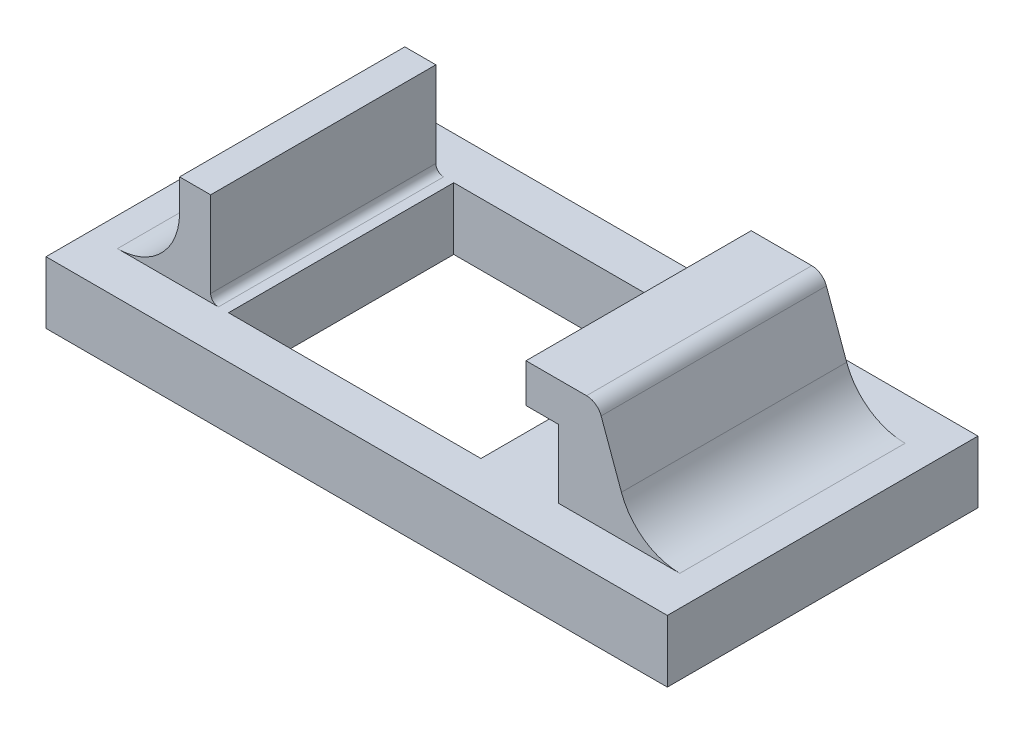
SolidWorks part; units mm, degrees
ref_plane "Front Plane" through (0, 0, 0) normal (0, 0, 1) x (1, 0, 0)
ref_plane "Top Plane" through (0, 0, 0) normal (0, 1, 0) x (1, 0, 0)
ref_plane "Right Plane" through (0, 0, 0) normal (1, 0, 0) x (0, 0, -1)
sketch "Sketch1" plane through (0, 0, 0) normal (0, 1, 0) x (1, 0, 0)
  line L1 (-20, 10) -> (20, 10)
  line L2 (-20, 10) -> (-20, -10)
  line L3 (-20, -10) -> (20, -10)
  line L4 (20, 10) -> (20, -10)
  line L5 (-20, 10) -> (20, -10) construction
  line L6 (-20, -10) -> (20, 10) construction
  point P0 (0, 0)
  dimension "D1" = 40
  dimension "D2" = 20
extrude "Boss-Extrude1" add sketch "Sketch1" along normal blind 4
sketch "Sketch2" plane through (0, 4, 0) normal (0, 1, 0) x (1, 0, 0)
  line L0 (-20, 10) -> (-20, -10) construction
  line L1 (-11, 7.25) -> (5.25, 7.25)
  line L2 (-11, 7.25) -> (-11, -7.25)
  line L3 (-11, -7.25) -> (5.25, -7.25)
  line L4 (5.25, 7.25) -> (5.25, -7.25)
  line L5 (-11, 7.25) -> (5.25, -7.25) construction
  line L6 (-11, -7.25) -> (5.25, 7.25) construction
  point P0 (-2.875, 0)
  dimension "D1" = 14.5
  dimension "D2" = 16.25
  dimension "D3" = 9
extrude "Cut-Extrude2" cut sketch "Sketch2" against normal blind 3.5
sketch "Sketch3" plane through (0, 0.5, 0) normal (0, 1, 0) x (1, 0, 0)
  line L0 (-11, -7.25) -> (5.25, -7.25) construction
  line L1 (-11, 7.25) -> (4.25, 7.25)
  line L2 (-11, 7.25) -> (-11, -7.25)
  line L3 (-11, -7.25) -> (4.25, -7.25)
  line L4 (4.25, 7.25) -> (4.25, -7.25)
  dimension "D1" = 15.25
extrude "Cut-Extrude3" cut sketch "Sketch3" against normal blind 0.5
sketch "Sketch4" plane through (0, 4, 0) normal (0, 1, 0) x (1, 0, 0)
  line L0 (5.25, 7.25) -> (-11, 7.25) construction
  line L1 (-12.15, 7.25) -> (-14.15, 7.25)
  line L2 (-12.15, 7.25) -> (-12.15, -7.25)
  line L3 (-12.15, -7.25) -> (-14.15, -7.25)
  line L4 (-14.15, 7.25) -> (-14.15, -7.25)
  line L5 (-11, -7.25) -> (5.25, -7.25) construction
  line L6 (-11, 7.25) -> (-11, -7.25) construction
  dimension "D1" = 1.15
  dimension "D2" = 2
extrude "Boss-Extrude2" add sketch "Sketch4" along normal blind 6
fillet "Fillet1" radius 4 1 edges at (-14.15, 4, 0)
fillet "Fillet2" radius 0.5 1 edges at (-12.15, 4, 0)
sketch "Sketch5" plane through (0, 4, 0) normal (0, 1, 0) x (1, 0, 0)
  line L0 (5.25, 7.25) -> (-11, 7.25) construction
  line L1 (10.25, 7.25) -> (12.75, 7.25)
  line L2 (10.25, 7.25) -> (10.25, -7.25)
  line L3 (10.25, -7.25) -> (12.75, -7.25)
  line L4 (12.75, 7.25) -> (12.75, -7.25)
  line L5 (-11, -7.25) -> (5.25, -7.25) construction
  line L6 (5.25, -7.25) -> (5.25, 7.25) construction
  dimension "D1" = 2.5
  dimension "D2" = 5
extrude "Boss-Extrude3" add sketch "Sketch5" along normal blind 4.4
sketch "Sketch6" plane through (0, 8.4, 0) normal (0, 1, 0) x (1, 0, 0)
  line L1 (12.75, 7.25) -> (8.15, 7.25)
  line L2 (12.75, 7.25) -> (12.75, -7.25)
  line L3 (12.75, -7.25) -> (8.15, -7.25)
  line L4 (8.15, 7.25) -> (8.15, -7.25)
  dimension "D1" = 4.6
extrude "Boss-Extrude4" add sketch "Sketch6" along normal blind 2.5
sketch "Sketch7" plane through (0, 0, 7.25) normal (0, 0, 1) x (1, 0, 0)
  line L0 (12.75, 4) -> (15.25, 4)
  line L1 (-20, 4) -> (20, 4) construction
  line L2 (12.75, 4) -> (12.75, 10.9)
  line L3 (12.75, 10.9) -> (15.25, 4)
  dimension "D1" = 2.5
extrude "Boss-Extrude5" add sketch "Sketch7" against normal blind 14.5
fillet "Fillet3" radius 1 1 edges at (12.75, 10.9, 0)
fillet "Fillet4" radius 4 1 edges at (15.25, 4, 0)
